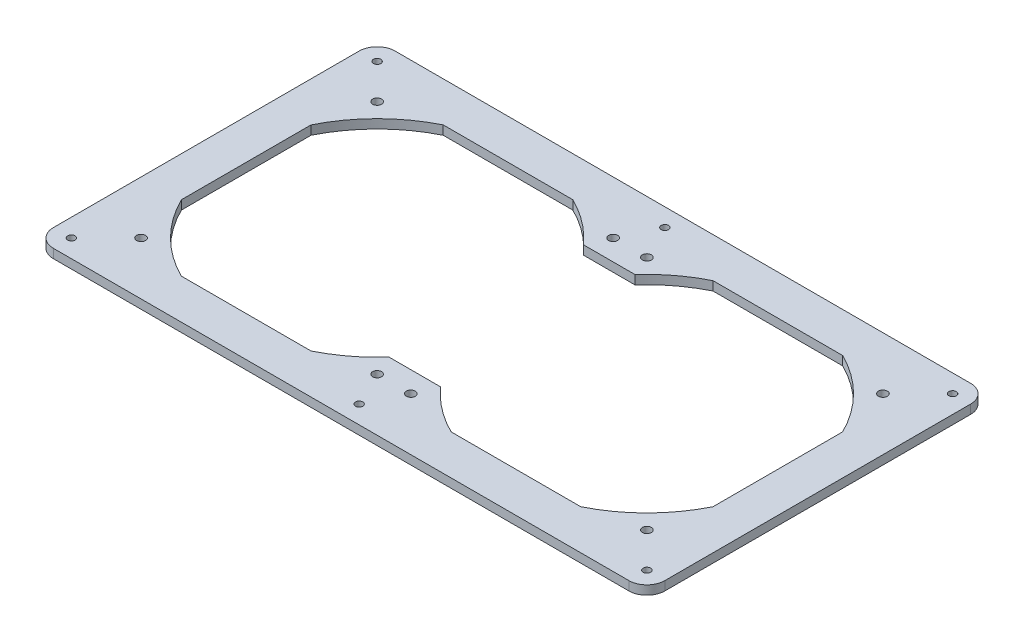
SolidWorks part; units mm, degrees
ref_plane "Front Plane" through (0, 0, 0) normal (0, 0, 1) x (1, 0, 0)
ref_plane "Top Plane" through (0, 0, 0) normal (0, 1, 0) x (1, 0, 0)
ref_plane "Right Plane" through (0, 0, 0) normal (1, 0, 0) x (0, 0, -1)
sketch "Sketch1" plane through (0, 0, 0) normal (0, 1, 0) x (1, 0, 0)
  line L0 (-55, 0) -> (55, 0) construction
  line L1 (60, -60) -> (-60, -60)
  line L2 (60, -60) -> (60, 60)
  line L3 (60, 60) -> (-60, 60)
  line L4 (-60, -60) -> (-60, 60)
  line L5 (60, -60) -> (-60, 60) construction
  line L6 (60, 60) -> (-60, -60) construction
  line L7 (52.5, -52.5) -> (-52.5, -52.5) construction
  line L8 (52.5, -52.5) -> (52.5, 52.5) construction
  line L9 (52.5, 52.5) -> (-52.5, 52.5) construction
  line L10 (-52.5, -52.5) -> (-52.5, 52.5) construction
  line L11 (52.5, -52.5) -> (-52.5, 52.5) construction
  line L12 (52.5, 52.5) -> (-52.5, -52.5) construction
  line L13 (58.25, -58.25) -> (-58.25, -58.25)
  line L14 (58.25, -58.25) -> (58.25, 58.25)
  line L15 (58.25, 58.25) -> (-58.25, 58.25)
  line L16 (-58.25, -58.25) -> (-58.25, 58.25)
  line L17 (58.25, -58.25) -> (-58.25, 58.25) construction
  line L18 (58.25, 58.25) -> (-58.25, -58.25) construction
  line L19 (0, -55) -> (0, 55) construction
  circle A0 centre (0, 0) radius 65 construction
  arc A1 (-58.25, 28.8433) -> (-28.8433, 58.25) centre (0, 0) cw
  circle A2 centre (-52.5, 52.5) radius 2
  circle A3 centre (-52.5, -52.5) radius 2
  arc A4 (-58.25, -28.8433) -> (-28.8433, -58.25) centre (0, 0) ccw
  circle A5 centre (52.5, -52.5) radius 2
  arc A6 (58.25, -28.8433) -> (28.8433, -58.25) centre (0, 0) cw
  circle A7 centre (52.5, 52.5) radius 2
  arc A8 (58.25, 28.8433) -> (28.8433, 58.25) centre (0, 0) ccw
  dimension "D1" = 130
  dimension "D5" = 4
  dimension "D2" = 120
  dimension "D3" = 105
  dimension "D4" = 116.5
extrude "Boss-Extrude1" add sketch "Sketch1" along normal blind 4 contours A4 L16 L13 A3 | L4 L1 L2 L3 L13 L16 L15 L14 | L16 A1 L15 A2 | A8 L14 L15 A7 | L14 A6 L13 A5
mirror "Mirror1" about plane through (60, 4, 0) normal (-1, 0, 0) of "Boss-Extrude1"
sketch "Sketch2" plane through (0, 0, 0) normal (0, 1, 0) x (1, 0, 0)
  line L4 (-60, 60) -> (-76, 76) construction
  line L5 (60, 60) -> (60, 76) construction
  line L6 (180, 60) -> (196, 76) construction
  line L7 (-2.2, 0) -> (2.2, 0) construction
  line L8 (-76, 76) -> (-76, -76)
  line L9 (-76, -76) -> (196, -76)
  line L10 (196, -76) -> (196, 76)
  line L11 (196, 76) -> (-76, 76)
  line L12 (-76, 76) -> (-76, -76)
  line L13 (-76, -76) -> (196, -76)
  line L14 (196, -76) -> (196, 76)
  line L15 (196, 76) -> (-76, 76)
  line L16 (-60, 60) -> (-60, -60)
  line L17 (-60, -60) -> (180, -60)
  line L18 (180, -60) -> (180, 60)
  line L19 (180, 60) -> (-60, 60)
  line L20 (-60, 60) -> (-60, -60)
  line L21 (-60, -60) -> (180, -60)
  line L22 (180, -60) -> (180, 60)
  line L23 (180, 60) -> (-60, 60)
  circle A0 centre (188, 68) radius 1.65
  circle A1 centre (60, 68) radius 1.65
  circle A2 centre (-68, 68) radius 1.65
  circle A3 centre (-68, -68) radius 1.65
  circle A4 centre (60, -68) radius 1.65
  circle A5 centre (188, -68) radius 1.65
  dimension "D3" = 3.3
  dimension "D1" = 16
  dimension "D2" = 0
extrude "Boss-Extrude2" add sketch "Sketch2" along normal blind 4
fillet "Fillet1" radius 8 4 edges at (196, 2, -76) (-76, 2, -76) (-76, 2, 76) (196, 2, 76)
sketch "Sketch3" plane through (0, 0, 0) normal (0, 1, 0) x (1, 0, 0)
  line L0 (58.25, 28.8433) -> (61.75, -28.8433) construction
  line L1 (67.5, 52.5) -> (74.0381, 45.9619) construction
  line L2 (0, -43.2538) -> (120, -43.2538)
  line L3 (0, -43.2538) -> (0, 43.2538)
  line L4 (0, 43.2538) -> (120, 43.2538)
  line L5 (120, -43.2538) -> (120, 43.2538)
  line L6 (0, -43.2538) -> (120, 43.2538) construction
  line L7 (0, 43.2538) -> (120, -43.2538) construction
  line L8 (67.5, 52.5) -> (67.5, 43.2538) construction
  arc A0 (91.1567, 58.25) -> (61.75, 28.8433) centre (120, 0) ccw construction
  point P4 (60, 0)
extrude "Cut-Extrude3" cut sketch "Sketch3" along normal through all contours L2 L5 L4 L3
